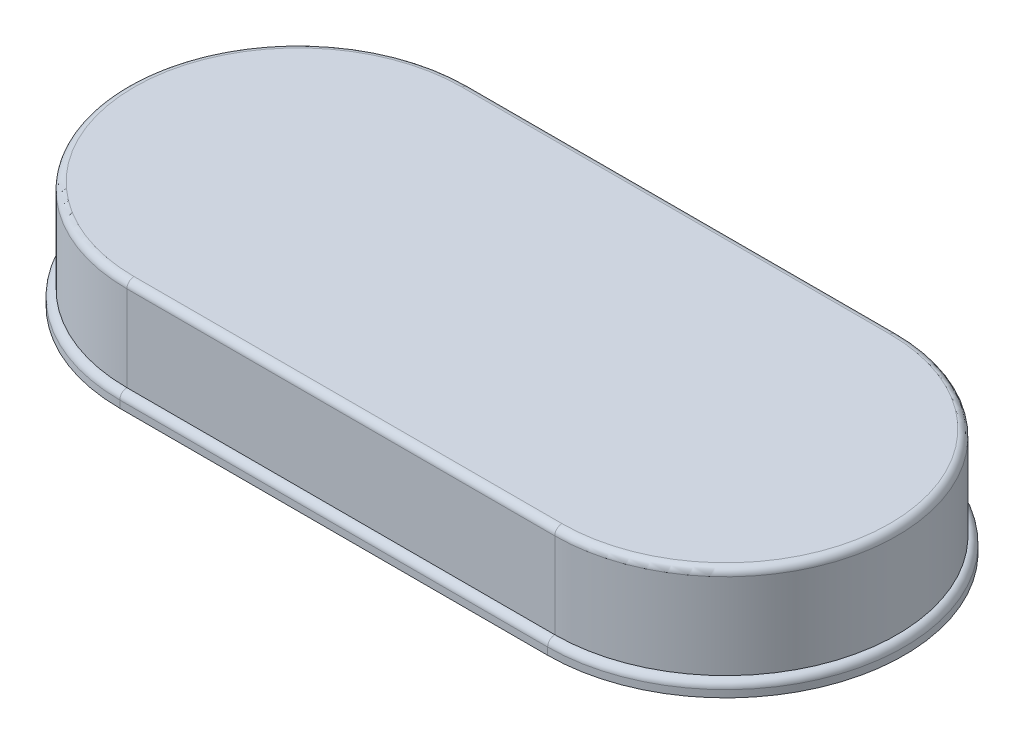
SolidWorks part; units mm, degrees
material "1060 Alloy"
ref_plane "Front Plane" through (0, 0, 0) normal (0, 0, 1) x (1, 0, 0)
ref_plane "Top Plane" through (0, 0, 0) normal (0, 1, 0) x (1, 0, 0)
ref_plane "Right Plane" through (0, 0, 0) normal (1, 0, 0) x (0, 0, -1)
sketch "Sketch2" plane through (0, 0, 0) normal (0, 1, 0) x (1, 0, 0)
  line L0 (8.7746, 14.8727) -> (8.7746, 9.8727) construction
  line L4 (8.7746, 14.8727) -> (14.7746, 14.8727)
  line L5 (11.7746, 14.8727) -> (11.7746, 12.8727) construction
  line L6 (14.7746, 14.8727) -> (14.7746, 9.8727) construction
  line L7 (8.7746, 9.8727) -> (14.7746, 9.8727)
  arc A0 (8.7746, 14.8727) -> (8.7746, 9.8727) centre (8.7746, 12.3727) ccw
  arc A1 (14.7746, 14.8727) -> (14.7746, 9.8727) centre (14.7746, 12.3727) cw
  point P0 (6.2746, 12.3727)
  point P1 (17.2746, 12.3727)
  dimension "D2" = 11
  dimension "D1" = 5
extrude "Boss-Extrude1" add sketch "Sketch2" along normal blind 0.2
fillet "Fillet3" radius 0.1 4 edges at (11.7746, 0.2, -14.8727) (17.2746, 0.2, -12.3727) (11.7746, 0.2, -9.8727) (6.2746, 0.2, -12.3727)
sketch "Sketch5" plane through (0, 0.2, 0) normal (0, 1, 0) x (1, 0, 0)
  line L0 (8.7746, 14.7727) -> (14.7746, 14.7727)
  line L1 (14.7746, 14.7727) -> (8.7746, 14.7727) construction
  line L2 (8.7746, 9.9727) -> (14.7746, 9.9727)
  line L3 (8.7746, 9.9727) -> (14.7746, 9.9727) construction
  line L4 (11.7746, 14.7727) -> (11.7746, 9.9727) construction
  arc A0 (8.7746, 9.9727) -> (8.7746, 14.7727) centre (8.7746, 12.3727) cw
  arc A1 (14.7746, 9.9727) -> (14.7746, 14.7727) centre (14.7746, 12.3727) ccw
extrude "Boss-Extrude2" add sketch "Sketch5" along normal blind 1.3
fillet "Fillet4" radius 0.1 4 edges at (11.7746, 1.5, -14.7727) (17.1746, 1.5, -12.3727) (11.7746, 1.5, -9.9727) (6.3746, 1.5, -12.3727)
